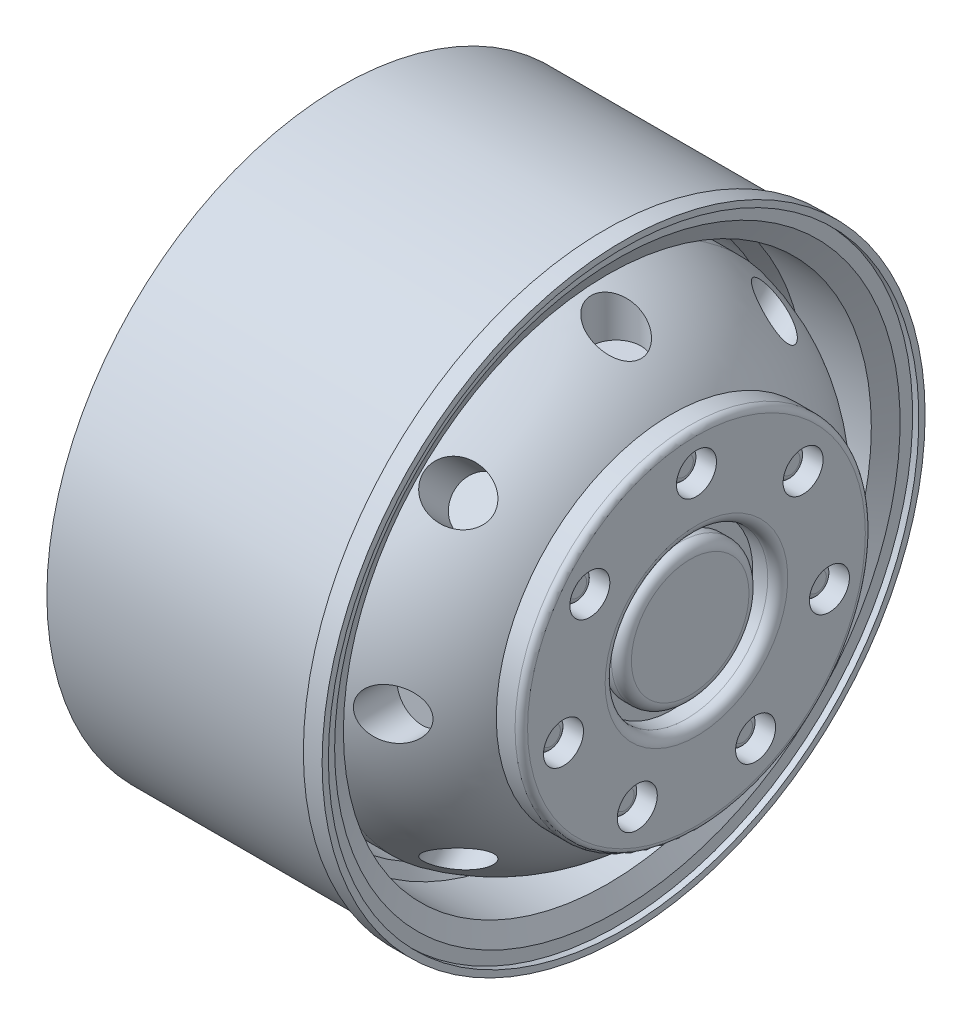
SolidWorks part; units mm, degrees
ref_plane "Front Plane" through (0, 0, 0) normal (0, 0, 1) x (1, 0, 0)
ref_plane "Top Plane" through (0, 0, 0) normal (0, 1, 0) x (1, 0, 0)
ref_plane "Right Plane" through (0, 0, 0) normal (1, 0, 0) x (0, 0, -1)
sketch "Sketch1" plane through (0, 0, 0) normal (0, 0, 1) x (1, 0, 0)
  line L0 (-25, 0) -> (25, 0) construction
  line L1 (0, 36.6286) -> (0, -30.4082) construction
  line L2 (-10, 23.5) -> (11.1, 23.5)
  line L3 (11.1, 23.5) -> (11.1, 24.1)
  line L4 (11.1, 24.1) -> (12.6, 24.1)
  line L5 (12.6, 24.1) -> (12.6, 23.6)
  line L9 (-10, 21.1) -> (-10, 23.5)
  line L10 (12.6, 23.6) -> (12.1, 23.6)
  line L11 (12.1, 23.6) -> (12.1, 22.6)
  line L12 (12.1, 22.6) -> (11.3, 21.1)
  line L15 (0, 20.1) -> (0, 19.6)
  line L16 (0, 19.6) -> (8, 19.6)
  line L20 (-1.5781, 0) -> (-1.4607, 16.5)
  line L24 (16.4219, 14) -> (18.4219, 14)
  line L25 (18.4219, 14) -> (18.4219, 0)
  line L27 (11.3, 21.1) -> (6, 21.1)
  line L28 (6, 21.1) -> (5.0157, 20.3)
  line L29 (5.0157, 20.3) -> (0, 20.1)
  line L30 (-10, 21.1) -> (-10, 16.5)
  line L31 (-10, 16.5) -> (-1.4607, 16.5)
  line L32 (-1.5781, 0) -> (18.4219, 0)
  arc A0 (8, 19.6) -> (16.4219, 14) centre (4.9727, 5.9143) cw
  dimension "D1" = 50
  dimension "D2" = 25
  dimension "D3" = 20
  dimension "D4" = 21.1
  dimension "D5" = 48.2
  dimension "D6" = 0.5
  dimension "D7" = 1.5
  dimension "D8" = 1
  dimension "D9" = 1
  dimension "D11" = 47
  dimension "D12" = 8
  dimension "D13" = 0.8
  dimension "D14" = 1.5
  dimension "D15" = 0.5
  dimension "D16" = 2
  dimension "D17" = 28
  dimension "D18" = 0.8
  dimension "D19" = 33
revolve "Revolve1" add sketch "Sketch1" angle 360 about L0
sketch "Sketch2" plane through (18.4219, 0, 0) normal (1, 0, 0) x (0, 0, -1)
  circle A0 centre (0, 0) radius 6.5
  circle A1 centre (0, 0) radius 10.9012 construction
  circle A2 centre (0, 10.9012) radius 1.6
  circle A3 centre (0, 0) radius 10.9012 construction
  circle A4 centre (8.5229, 6.7968) radius 1.6
  circle A5 centre (0, 0) radius 10.9012 construction
  circle A6 centre (10.6279, -2.4257) radius 1.6
  circle A7 centre (0, 0) radius 10.9012 construction
  circle A8 centre (4.7299, -9.8216) radius 1.6
  circle A9 centre (0, 0) radius 10.9012 construction
  circle A10 centre (-4.7299, -9.8216) radius 1.6
  circle A11 centre (0, 0) radius 10.9012 construction
  circle A12 centre (-10.6279, -2.4257) radius 1.6
  circle A13 centre (0, 0) radius 10.9012 construction
  circle A14 centre (-8.5229, 6.7968) radius 1.6
  point P18 (0, 0)
  dimension "D1" = 13
  dimension "D2" = 3.2
  dimension "D3" = 7
extrude "Cut-Extrude1" cut sketch "Sketch2" against normal blind 2
fillet "Fillet1" radius 0.5 1 edges at (18.4219, 0, 14)
sketch "Sketch3" plane through (16.4219, 0, 0) normal (1, 0, 0) x (0, 0, -1)
  line L0 (0, 12.5012) -> (0, 9.3012) construction
  line L1 (-1.6, 10.9012) -> (1.6, 10.9012) construction
  circle A0 centre (0, 10.9012) radius 1.6 construction
  circle A1 centre (0, 10.9012) radius 1.25
  circle A2 centre (8.5229, 6.7968) radius 1.25
  circle A3 centre (10.6279, -2.4257) radius 1.25
  circle A4 centre (4.7299, -9.8216) radius 1.25
  circle A5 centre (-4.7299, -9.8216) radius 1.25
  circle A6 centre (-10.6279, -2.4257) radius 1.25
  circle A7 centre (-8.5229, 6.7968) radius 1.25
  point P18 (0, 0)
  dimension "D1" = 2.5
  dimension "D2" = 7
extrude "Boss-Extrude1" add sketch "Sketch3" along normal blind 1
fillet "Fillet2" radius 0.5 7 edges at (17.4219, -9.8216, -5.9799) (17.4219, -2.4257, -11.8779) (17.4219, 6.7968, -9.7729) (17.4219, 10.9012, -1.25) (17.4219, -9.8216, 3.4799) (17.4219, 6.7968, 7.2729) (17.4219, -2.4257, 9.3779)
sketch "Sketch4" plane through (16.4219, 0, 0) normal (1, 0, 0) x (0, 0, -1)
  circle A2 centre (0, 0) radius 5.5
  circle A3 centre (0, 0) radius 5.5
  dimension "D1" = 1
extrude "Boss-Extrude2" add sketch "Sketch4" along normal blind 1.5
fillet "Fillet3" radius 0.8 1 edges at (17.9219, 0, -5.5)
fillet "Fillet4" radius 0.8 1 edges at (18.4219, 0, -6.5)
ref_plane "Plane1" through (0, 18, 0) normal (0, 1, 0) x (1, 0, 0)
sketch "Sketch6" plane through (0, 18, 0) normal (0, 1, 0) x (1, 0, 0)
  line L0 (0, 0) -> (0, -27.5865) construction
  circle A0 centre (12, 0) radius 2
  point P5 (0, 0)
  dimension "D2" = 4
  dimension "D1" = 12
extrude "Cut-Extrude2" cut sketch "Sketch6" against normal mid plane 5
pattern_circular "CirPattern1" count 8 over 360 about axis through (0, 0, 0) along (1, 0, 0) of "Cut-Extrude2"
